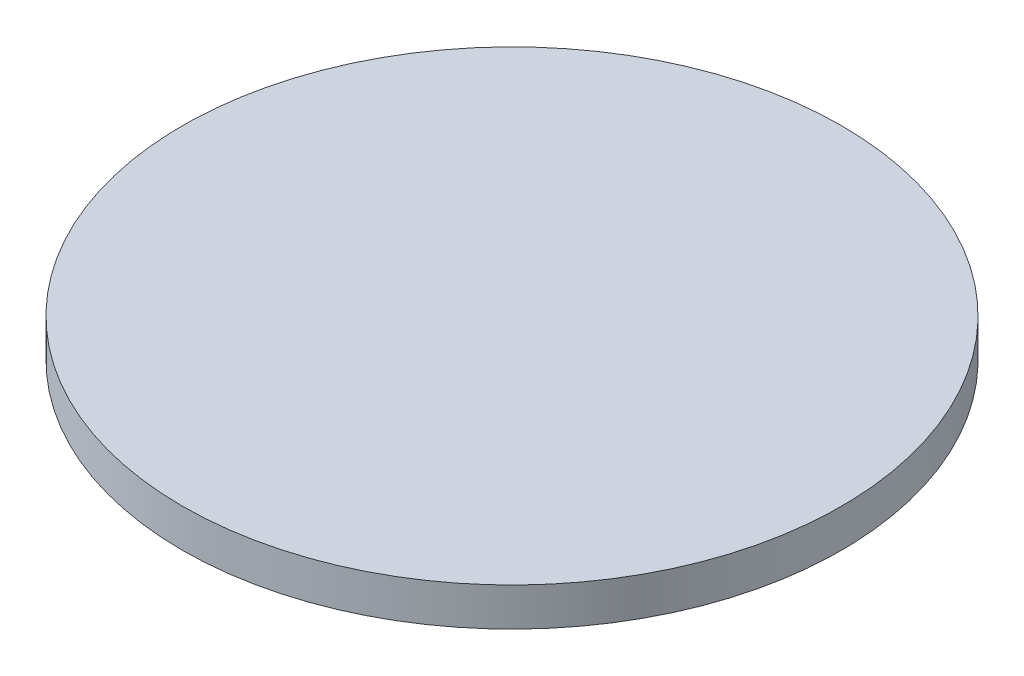
SolidWorks part; units mm, degrees
ref_plane "Front Plane" through (0, 0, 0) normal (0, 0, 1) x (1, 0, 0)
ref_plane "Top Plane" through (0, 0, 0) normal (0, 1, 0) x (1, 0, 0)
ref_plane "Right Plane" through (0, 0, 0) normal (1, 0, 0) x (0, 0, -1)
sketch "Sketch1" plane through (0, 0, 0) normal (0, 1, 0) x (1, 0, 0)
  circle A0 centre (0, 0) radius 109.5375
  dimension "D1" = 219.075
extrude "Extrude1" add sketch "Sketch1" along normal blind 12.7
